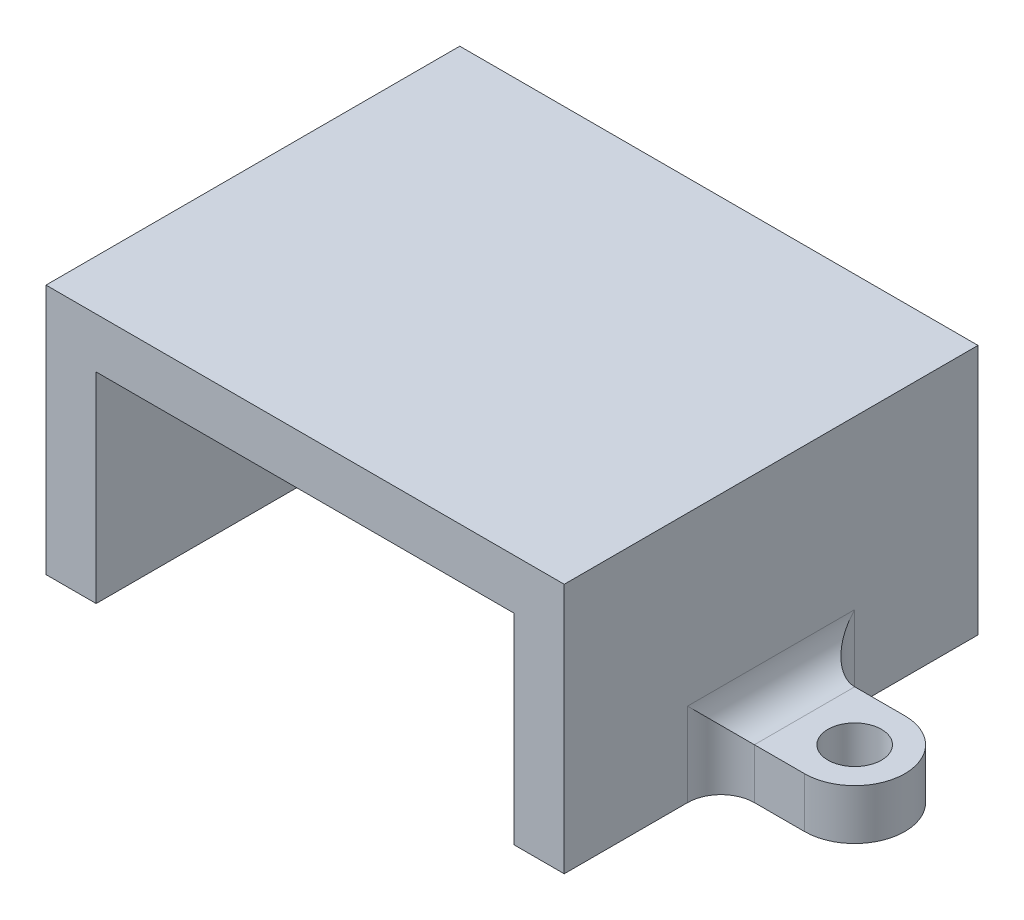
SolidWorks part; units mm, degrees
ref_plane "前视基准面" through (0, 0, 0) normal (0, 0, 1) x (1, 0, 0)
ref_plane "上视基准面" through (0, 0, 0) normal (0, 1, 0) x (1, 0, 0)
ref_plane "右视基准面" through (0, 0, 0) normal (1, 0, 0) x (0, 0, -1)
sketch "草图1" plane through (0, 0, 0) normal (0, 0, 1) x (1, 0, 0)
  line L0 (0, 0) -> (3, 0)
  line L1 (3, 0) -> (3, 12)
  line L2 (3, 12) -> (28, 12)
  line L3 (28, 12) -> (28, 0)
  line L4 (28, 0) -> (31, 0)
  line L5 (31, 0) -> (31, 15)
  line L6 (31, 15) -> (0, 15)
  line L7 (0, 15) -> (0, 0)
  dimension "D1" = 12
  dimension "D2" = 3
  dimension "D3" = 3
  dimension "D4" = 3
  dimension "D5" = 25
extrude "凸台-拉伸1" add sketch "草图1" along normal blind 24.75
sketch "草图2" plane through (0, 0, 0) normal (0, -1, 0) x (1, 0, 0)
  line L0 (15.5, 24.75) -> (15.5, -1.1402) construction
  line L1 (3, 24.75) -> (28, 24.75) construction
  line L2 (0, 12.375) -> (33.2336, 12.375) construction
  line L3 (0, 24.75) -> (0, 0) construction
  line L4 (36, 9.375) -> (31, 9.375)
  line L5 (31, 24.75) -> (31, 0) construction
  line L6 (31, 15.375) -> (31, 9.375)
  line L7 (0, 15.375) -> (0, 9.375)
  line L8 (-5, 9.375) -> (0, 9.375)
  line L9 (31, 15.375) -> (36, 15.375)
  line L10 (0, 15.375) -> (-5, 15.375)
  arc A0 (36, 9.375) -> (36, 15.375) centre (36, 12.375) ccw
  circle A1 centre (36, 12.375) radius 1.6
  circle A2 centre (-5, 12.375) radius 1.6
  arc A3 (-5, 9.375) -> (-5, 15.375) centre (-5, 12.375) cw
  dimension "D1" = 6
  dimension "D2" = 3.2
  dimension "D3" = 5
extrude "凸台-拉伸2" add sketch "草图2" against normal blind 3
fillet "圆角1" radius 2 6 edges at (31, 1.5, 9.375) (31, 3, 12.375) (31, 1.5, 15.375) (0, 1.5, 9.375) (0, 1.5, 15.375) (0, 3, 12.375)
